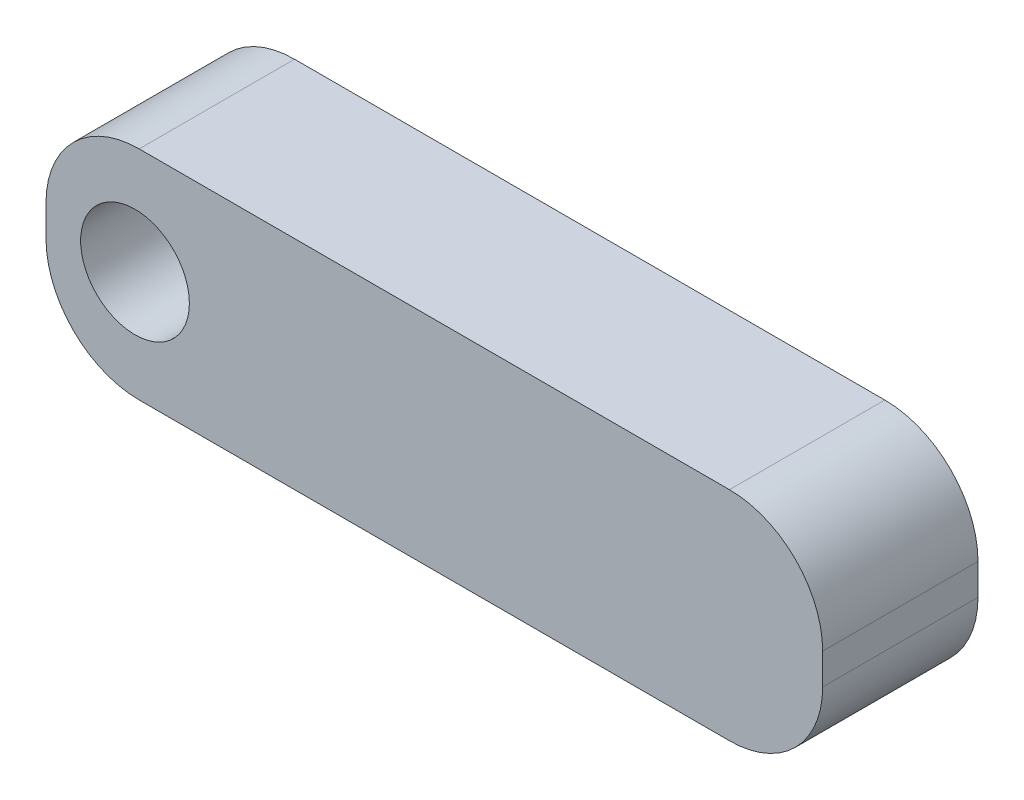
SolidWorks part; units mm, degrees
ref_plane "Front Plane" through (0, 0, 0) normal (0, 0, 1) x (1, 0, 0)
ref_plane "Top Plane" through (0, 0, 0) normal (0, 1, 0) x (1, 0, 0)
ref_plane "Right Plane" through (0, 0, 0) normal (1, 0, 0) x (0, 0, -1)
sketch "Sketch1" plane through (0, 0, 0) normal (0, 0, 1) x (1, 0, 0)
  line L1 (-12.5, -3.5) -> (12.5, -3.5)
  line L2 (-12.5, -3.5) -> (-12.5, 3.5)
  line L3 (-12.5, 3.5) -> (12.5, 3.5)
  line L4 (12.5, -3.5) -> (12.5, 3.5)
  line L5 (-12.5, -3.5) -> (12.5, 3.5) construction
  line L6 (-12.5, 3.5) -> (12.5, -3.5) construction
  circle A0 centre (-9.6354, 0) radius 1.75
  point P0 (0, 0)
  dimension "D3" = 3.5
  dimension "D1" = 7
  dimension "D2" = 25
extrude "Boss-Extrude1" add sketch "Sketch1" along normal blind 5
fillet "Fillet1" radius 3 2 edges at (-12.5, 3.5, 2.5) (-12.5, -3.5, 2.5)
fillet "Fillet2" radius 3 2 edges at (12.5, 3.5, 2.5) (12.5, -3.5, 2.5)
